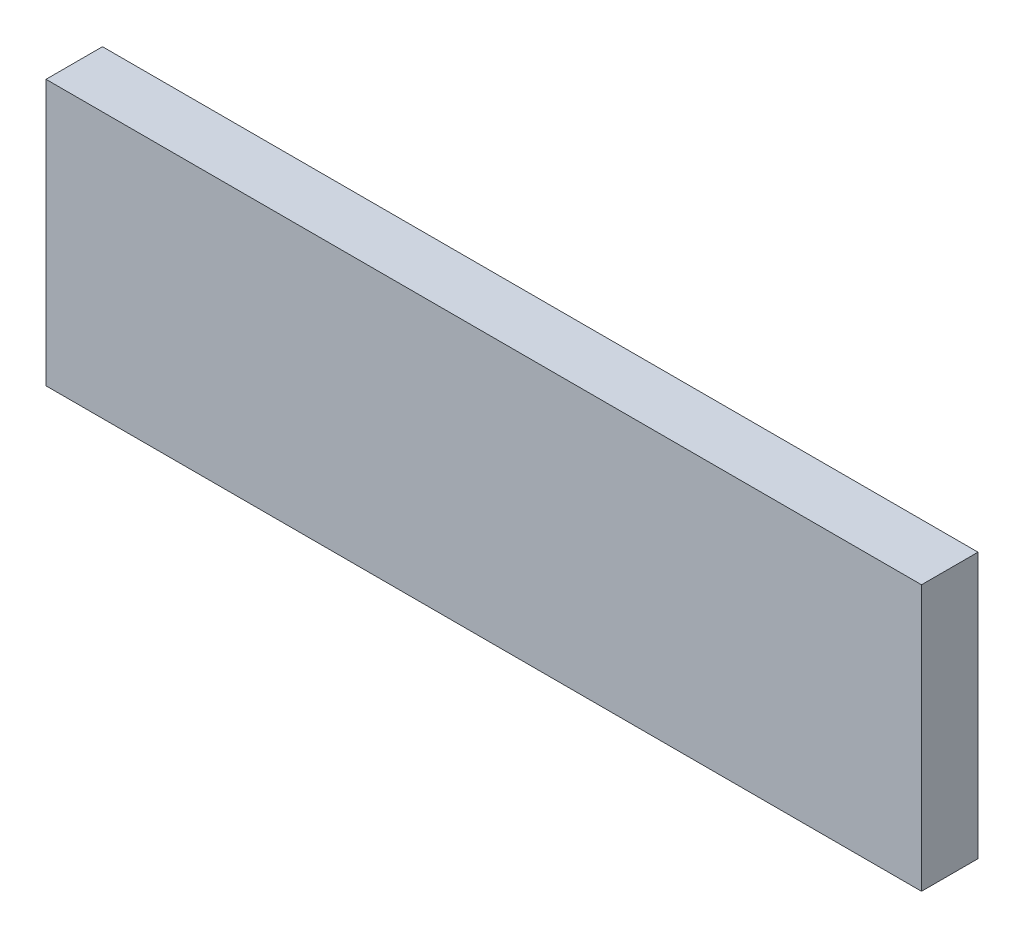
SolidWorks part; units mm, degrees
material "Plain Carbon Steel"
ref_plane "Front Plane" through (0, 0, 0) normal (0, 0, 1) x (1, 0, 0)
ref_plane "Top Plane" through (0, 0, 0) normal (0, 1, 0) x (1, 0, 0)
ref_plane "Right Plane" through (0, 0, 0) normal (1, 0, 0) x (0, 0, -1)
sketch "Sketch1" plane through (0, 0, 0) normal (0, 0, 1) x (1, 0, 0)
  line L1 (0, 0) -> (155, 0)
  line L2 (0, 0) -> (0, 47)
  line L3 (0, 47) -> (155, 47)
  line L4 (155, 0) -> (155, 47)
  dimension "D1" = 155
  dimension "D2" = 47
extrude "Boss-Extrude1" add sketch "Sketch1" along normal blind 10
